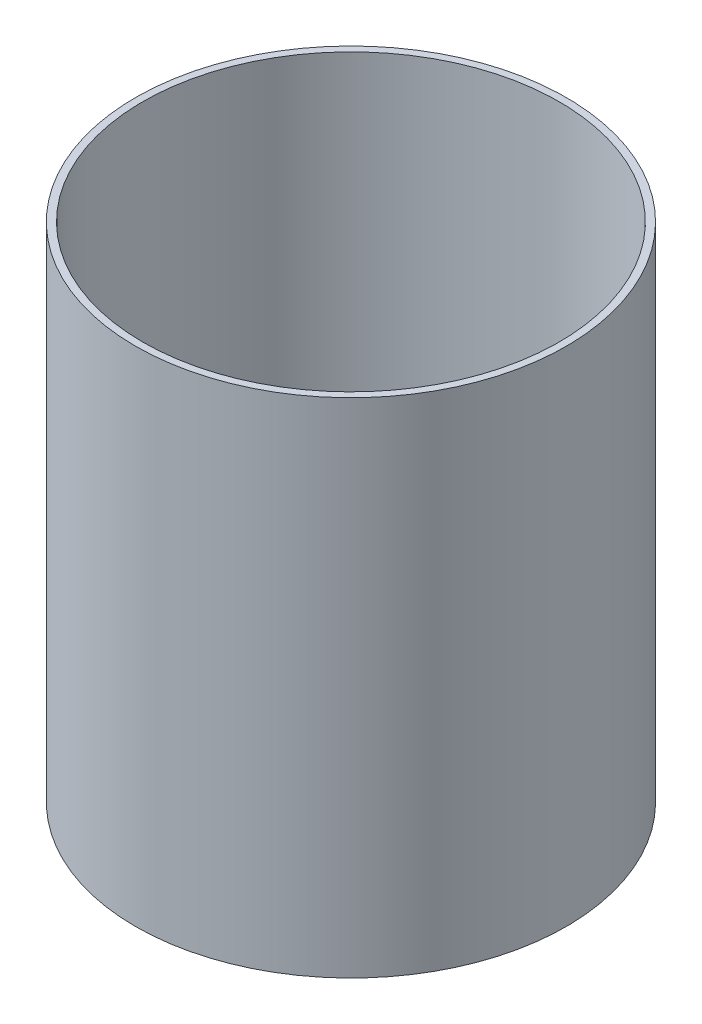
SolidWorks part; units mm, degrees
ref_plane "Front Plane" through (0, 0, 0) normal (0, 0, 1) x (1, 0, 0)
ref_plane "Top Plane" through (0, 0, 0) normal (0, 1, 0) x (1, 0, 0)
ref_plane "Right Plane" through (0, 0, 0) normal (1, 0, 0) x (0, 0, -1)
sketch "Sketch1" plane through (0, 0, 0) normal (0, 1, 0) x (1, 0, 0)
  circle A0 centre (0, 0) radius 38.1
  circle A1 centre (0, 0) radius 36.83
  dimension "D1" = 76.2
  dimension "D2" = 73.66
extrude "Boss-Extrude1" add sketch "Sketch1" along normal blind 88.9
